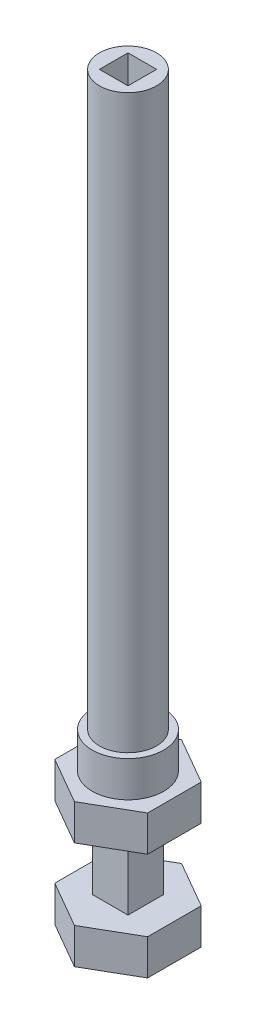
SolidWorks part; units mm, degrees
ref_plane "Front Plane" through (0, 0, 0) normal (0, 0, 1) x (1, 0, 0)
ref_plane "Top Plane" through (0, 0, 0) normal (0, 1, 0) x (1, 0, 0)
ref_plane "Right Plane" through (0, 0, 0) normal (1, 0, 0) x (0, 0, -1)
sketch "Sketch1" plane through (0, 0, 0) normal (0, 1, 0) x (1, 0, 0)
  line L1 (2.5, -2.5) -> (-2.5, -2.5)
  line L2 (2.5, -2.5) -> (2.5, 2.5)
  line L3 (2.5, 2.5) -> (-2.5, 2.5)
  line L4 (-2.5, -2.5) -> (-2.5, 2.5)
  line L5 (2.5, -2.5) -> (-2.5, 2.5) construction
  line L6 (2.5, 2.5) -> (-2.5, -2.5) construction
  point P0 (0, 0)
  dimension "D1" = 5
  dimension "D2" = 5
extrude "Boss-Extrude1" add sketch "Sketch1" along normal blind 10
sketch "Sketch2" plane through (0, 0, 0) normal (0, -1, 0) x (1, 0, 0)
  line L5 (0, 7.5) -> (-6.4952, 3.75)
  line L6 (-6.4952, 3.75) -> (-6.4952, -3.75)
  line L7 (-6.4952, -3.75) -> (0, -7.5)
  line L8 (0, -7.5) -> (6.4952, -3.75)
  line L9 (6.4952, -3.75) -> (6.4952, 3.75)
  line L10 (6.4952, 3.75) -> (0, 7.5)
  circle A0 centre (0, 0) radius 6.4952 construction
  point P0 (0, 0)
  dimension "D1" = 15
extrude "Boss-Extrude2" add sketch "Sketch2" along normal blind 5
sketch "Sketch3" plane through (0, 10, 0) normal (0, 1, 0) x (1, 0, 0)
  line L6 (0, -7.5) -> (6.4952, -3.75)
  line L7 (6.4952, -3.75) -> (6.4952, 3.75)
  line L8 (6.4952, 3.75) -> (0, 7.5)
  line L9 (0, 7.5) -> (-6.4952, 3.75)
  line L10 (-6.4952, 3.75) -> (-6.4952, -3.75)
  line L11 (-6.4952, -3.75) -> (0, -7.5)
  line L12 (0, -7.5) -> (6.4952, -3.75)
  line L13 (6.4952, -3.75) -> (6.4952, 3.75)
  line L14 (6.4952, 3.75) -> (0, 7.5)
  line L15 (0, 7.5) -> (-6.4952, 3.75)
  line L16 (-6.4952, 3.75) -> (-6.4952, -3.75)
  line L17 (-6.4952, -3.75) -> (0, -7.5)
  dimension "D1" = 0
extrude "Boss-Extrude3" add sketch "Sketch3" along normal blind 5
sketch "Sketch4" plane through (0, 15, 0) normal (0, 1, 0) x (1, 0, 0)
  circle A0 centre (0, 0) radius 5
  dimension "D1" = 10
extrude "Boss-Extrude4" add sketch "Sketch4" along normal blind 5
sketch "Sketch5" plane through (0, 20, 0) normal (0, 1, 0) x (1, 0, 0)
  circle A0 centre (0, 0) radius 4
  dimension "D1" = 8
extrude "Boss-Extrude5" add sketch "Sketch5" along normal offset from surface (80 mm away) 90 up to face at (0, 10, 0)
sketch "Sketch6" plane through (0, 100, 0) normal (0, 1, 0) x (1, 0, 0)
  line L1 (2, -2) -> (-2, -2)
  line L2 (2, -2) -> (2, 2)
  line L3 (2, 2) -> (-2, 2)
  line L4 (-2, -2) -> (-2, 2)
  line L5 (2, -2) -> (-2, 2) construction
  line L6 (2, 2) -> (-2, -2) construction
  point P0 (0, 0)
  dimension "D1" = 4
  dimension "D2" = 4
extrude "Cut-Extrude1" cut sketch "Sketch6" against normal blind 4
